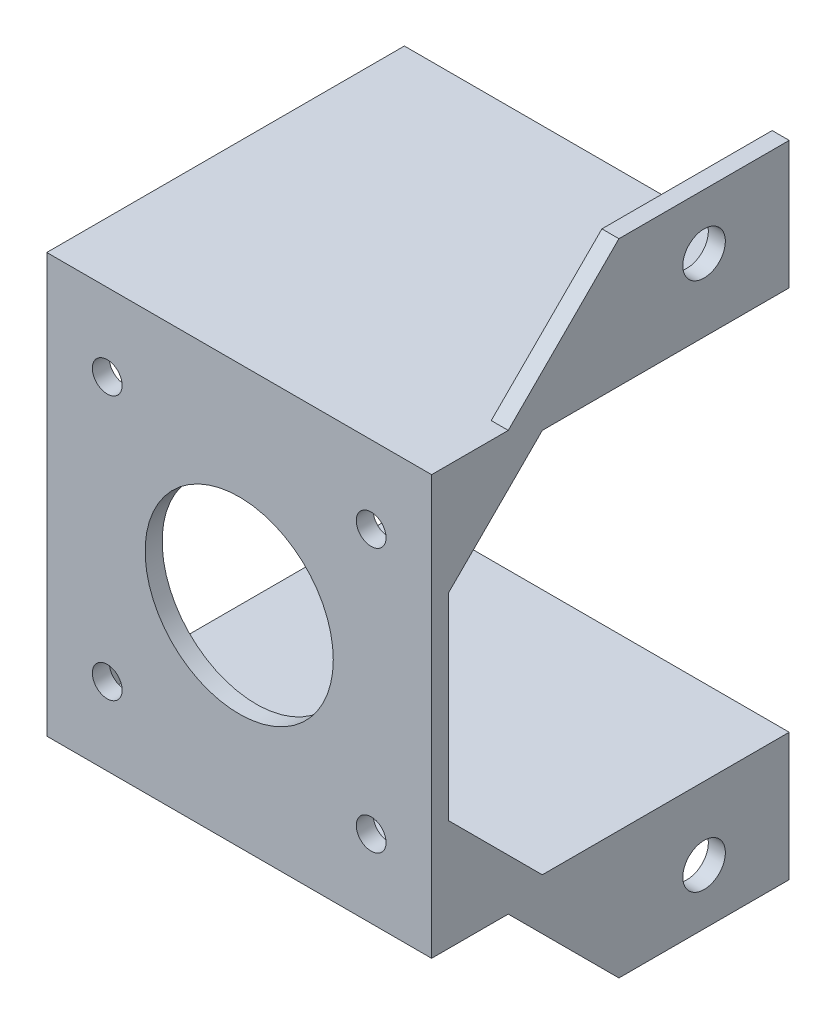
SolidWorks part; units mm, degrees
ref_plane "Front Plane" through (0, 0, 0) normal (0, 0, 1) x (1, 0, 0)
ref_plane "Top Plane" through (0, 0, 0) normal (0, 1, 0) x (1, 0, 0)
ref_plane "Right Plane" through (0, 0, 0) normal (1, 0, 0) x (0, 0, -1)
sketch "Sketch1" plane through (0, 0, 0) normal (0, 0, 1) x (1, 0, 0)
  line L1 (-22.6, -22.6) -> (22.6, -22.6)
  line L2 (-22.6, -22.6) -> (-22.6, 22.6)
  line L3 (-22.6, 22.6) -> (22.6, 22.6)
  line L4 (22.6, -22.6) -> (22.6, 22.6)
  line L5 (-22.6, -22.6) -> (22.6, 22.6) construction
  line L6 (-22.6, 22.6) -> (22.6, -22.6) construction
  circle A0 centre (-15.5, 15.5) radius 1.75
  circle A1 centre (15.5, 15.5) radius 1.75
  circle A2 centre (-15.5, -15.5) radius 1.75
  circle A3 centre (15.5, -15.5) radius 1.75
  circle A4 centre (0, 0) radius 11.05
  point P0 (0, 0)
  dimension "D1" = 3.5
  dimension "D2" = 31
  dimension "D3" = 31
  dimension "D5" = 22.1
  dimension "D4" = 45.2
extrude "Boss-Extrude1" add sketch "Sketch1" along normal blind 2
sketch "Sketch3" plane through (0, 0, 2) normal (0, 0, 1) x (1, 0, 0)
  line L0 (-22.6, 22.6) -> (22.6, 22.6)
  line L1 (22.6, 22.6) -> (22.6, 24.6)
  line L2 (22.6, 24.6) -> (-22.6, 24.6)
  line L3 (-22.6, 24.6) -> (-22.6, 22.6)
  dimension "D1" = 2
extrude "Boss-Extrude2" add sketch "Sketch3" against normal blind 42
sketch "Sketch4" plane through (22.6, 0, 0) normal (1, 0, 0) x (0, 0, -1)
  line L0 (40, 22.6) -> (0, 22.6) construction
  line L1 (40, 24.6) -> (20, 24.6)
  line L2 (40, 24.6) -> (40, 37.6)
  line L3 (40, 37.6) -> (20, 37.6)
  line L4 (20, 24.6) -> (20, 37.6)
  line L5 (20, 37.6) -> (7, 24.6)
  line L6 (40, 24.6) -> (-2, 24.6) construction
  line L7 (7, 24.6) -> (20, 24.6)
  circle A0 centre (30, 31.1) radius 2.5
  point P10 (30, 37.6)
  point P11 (40, 31.1)
  line M9 (40, 24.6) -> (-2, 24.6)
  dimension "D3" = 5
  dimension "D1" = 20
  dimension "D2" = 15
  dimension "D4" = 45
extrude "Boss-Extrude3" add sketch "Sketch4" against normal blind 2 contours L4 L5 M9 | L4 L2 L3 A0 M9
mirror "Mirror1" about plane through (0, 0, 0) normal (0, 1, 0) of "Boss-Extrude2", "Boss-Extrude3"
sketch "Sketch5" plane through (-22.6, 0, 0) normal (-1, 0, 0) x (0, 0, 1)
  line L0 (-13, 24.6) -> (2, 9.6)
  line L1 (-40, 24.6) -> (2, 24.6) construction
  line L2 (2, 24.6) -> (2, -24.6) construction
  line L3 (2, 9.6) -> (2, 24.6)
  line L4 (2, 24.6) -> (-13, 24.6)
  line L5 (-13, -24.6) -> (2, -9.6)
  line L6 (-40, -24.6) -> (2, -24.6) construction
  line L7 (2, -9.6) -> (2, -24.6)
  line L8 (2, -24.6) -> (-13, -24.6)
  dimension "D1" = 15
extrude "Boss-Extrude4" add sketch "Sketch5" against normal blind 1
sketch "Sketch6" plane through (22.6, 0, 0) normal (1, 0, 0) x (0, 0, -1)
  line L0 (-2, 9.6) -> (13, 24.6)
  line L1 (-2, -24.6) -> (-2, 24.6) construction
  line L2 (7, 24.6) -> (-2, 24.6) construction
  line L3 (13, 24.6) -> (-2, 24.6)
  line L4 (-2, 24.6) -> (-2, 9.6)
  line L5 (13, -24.6) -> (-2, -9.6)
  line L6 (7, -24.6) -> (-2, -24.6) construction
  line L7 (-2, -9.6) -> (-2, -24.6)
  line L8 (-2, -24.6) -> (13, -24.6)
  dimension "D1" = 15
extrude "Boss-Extrude5" add sketch "Sketch6" against normal blind 1
